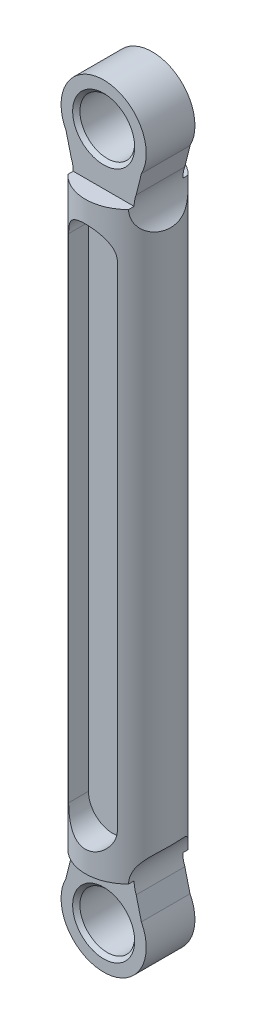
SolidWorks part; units mm, degrees
ref_plane "Front Plane" through (0, 0, 0) normal (0, 0, 1) x (1, 0, 0)
ref_plane "Top Plane" through (0, 0, 0) normal (0, 1, 0) x (1, 0, 0)
ref_plane "Right Plane" through (0, 0, 0) normal (1, 0, 0) x (0, 0, -1)
sketch "Sketch1" plane through (0, 0, 0) normal (0, 1, 0) x (1, 0, 0)
  circle A0 centre (0, 0) radius 3.5
  dimension "D1" = 7
extrude "Extrude1" add sketch "Sketch1" along normal blind 48
sketch "Sketch3" plane through (0, 48, 0) normal (0, 1, 0) x (1, 0, 0)
  line L1 (-4, 2) -> (4, 2)
  line L2 (-4, 2) -> (-4, -2)
  line L3 (-4, -2) -> (4, -2)
  line L4 (4, 2) -> (4, -2)
  dimension "D1" = 2
  dimension "D2" = 4
  dimension "D3" = 8
  dimension "D4" = 4
extrude "Extrude2" add sketch "Sketch3" along normal blind 9
sketch "Sketch4" plane through (0, 0, 2) normal (0, 0, 1) x (1, 0, 0)
  line L0 (-7.5, 47.9879) -> (-8.5956, 58.1731)
  line L1 (-8.5956, 58.1731) -> (8.8583, 57.4951)
  line L2 (8.8583, 57.4951) -> (7.5, 47.9876)
  line L6 (3.0976, 50.6205) -> (2.673, 48.9013)
  line L7 (-3.0976, 50.6205) -> (-2.673, 48.9013)
  arc A0 (3.0976, 50.6205) -> (-3.0976, 50.6205) centre (0, 52.25) ccw
  arc A1 (2.673, 48.9013) -> (7.5, 47.9876) centre (5, 47.9876) ccw
  arc A2 (-7.5, 47.9879) -> (-2.6732, 48.9023) centre (-5, 47.9879) ccw
  circle A3 centre (0, 52.25) radius 2.25
  dimension "D1" = 7
  dimension "D4" = 5
  dimension "D5" = 5
extrude "Extrude3" cut sketch "Sketch4" against normal through all and the other way through all
sketch "Sketch5" plane through (0, 0, 0) normal (0, -1, 0) x (1, 0, 0)
  line L0 (-4, 2) -> (4, 2)
  line L1 (-4, 2) -> (-4, -2)
  line L2 (-4, -2) -> (4, -2)
  line L3 (4, 2) -> (4, -2)
  dimension "D1" = 4
  dimension "D2" = 8
  dimension "D3" = 2
  dimension "D4" = 4
extrude "Extrude4" add sketch "Sketch5" along normal blind 10
sketch "Sketch6" plane through (0, 0, -2) normal (0, 0, -1) x (-1, 0, 0)
  line L0 (-2.8723, 0) -> (2.8723, 0) construction
  line L1 (4, -10) -> (4, 0) construction
  line L6 (-3.0976, -2.6205) -> (-2.673, -0.9013)
  line L7 (3.0976, -2.6205) -> (2.673, -0.9013)
  line L8 (9.5126, -12.1306) -> (7.5, 0.0124)
  line L9 (-8.7007, -11.6442) -> (9.5126, -12.1306)
  line L10 (-7.5, 0.0121) -> (-8.7007, -11.6442)
  circle A4 centre (0, -4.25) radius 2.25
  arc A5 (-7.5, 0.0121) -> (-2.6732, -0.9023) centre (-5, 0.0121) cw
  arc A6 (2.673, -0.9013) -> (7.5, 0.0124) centre (5, 0.0124) cw
  arc A7 (3.0976, -2.6205) -> (-3.0976, -2.6205) centre (0, -4.25) cw
  dimension "D2" = 4.5
  dimension "D3" = 3.5
  dimension "D7" = 2.5
  dimension "D8" = 2.5
  dimension "D1" = 4.25
  dimension "D4" = 4
extrude "Extrude9" cut sketch "Sketch6" against normal through all and the other way through all
ref_plane "Plane1" through (0, 0, 3.5) normal (0, 0, 1) x (1, 0, 0)
sketch "Sketch7" plane through (0, 0, 3.5) normal (0, 0, 1) x (1, 0, 0)
  line L2 (-2, 44.25) -> (-2, 3.75)
  line L4 (2, 44.25) -> (2, 3.75)
  arc A0 (0, 46.25) -> (-2, 44.25) centre (0, 44.25) ccw
  arc A1 (2, 3.75) -> (0, 1.75) centre (0, 3.75) cw
  arc A2 (-2, 3.75) -> (2, 3.75) centre (0, 3.75) ccw
  arc A3 (2, 44.25) -> (-2, 44.25) centre (0, 44.25) ccw
  dimension "D6" = 2
  dimension "D7" = 2
  dimension "D1" = 40.5
  dimension "D2" = 2
  dimension "D3" = 4
extrude "Extrude10" cut sketch "Sketch7" against normal blind 2.25 contours L4 A3 A0 L2 A2 A1
ref_plane "Plane2" through (0, 0, -3.5) normal (0, 0, -1) x (-1, 0, 0)
sketch "Sketch8" plane through (0, 0, -3.5) normal (0, 0, -1) x (-1, 0, 0)
  line L0 (-2, 44.25) -> (-2, 3.75)
  line L1 (2, 44.25) -> (2, 3.75)
  line L2 (-2.5, 48) -> (2.5, 48) construction
  arc A2 (-2, 3.75) -> (2, 3.75) centre (0, 3.75) ccw
  arc A3 (2, 44.25) -> (-2, 44.25) centre (0, 44.25) ccw
  point P3 (0, 48)
  dimension "D2" = 2
  dimension "D3" = 2
  dimension "D5" = 3.75
  dimension "D1" = 40.5
  dimension "D4" = 4
extrude "Extrude11" cut sketch "Sketch8" against normal blind 2.25
chamfer "Chamfer1" distance 0.3 angle 45 4 edges at (-2.25, -4.25, 2) (2.25, -4.25, -2) (2.25, 52.25, -2) (-2.25, 52.25, 2)
